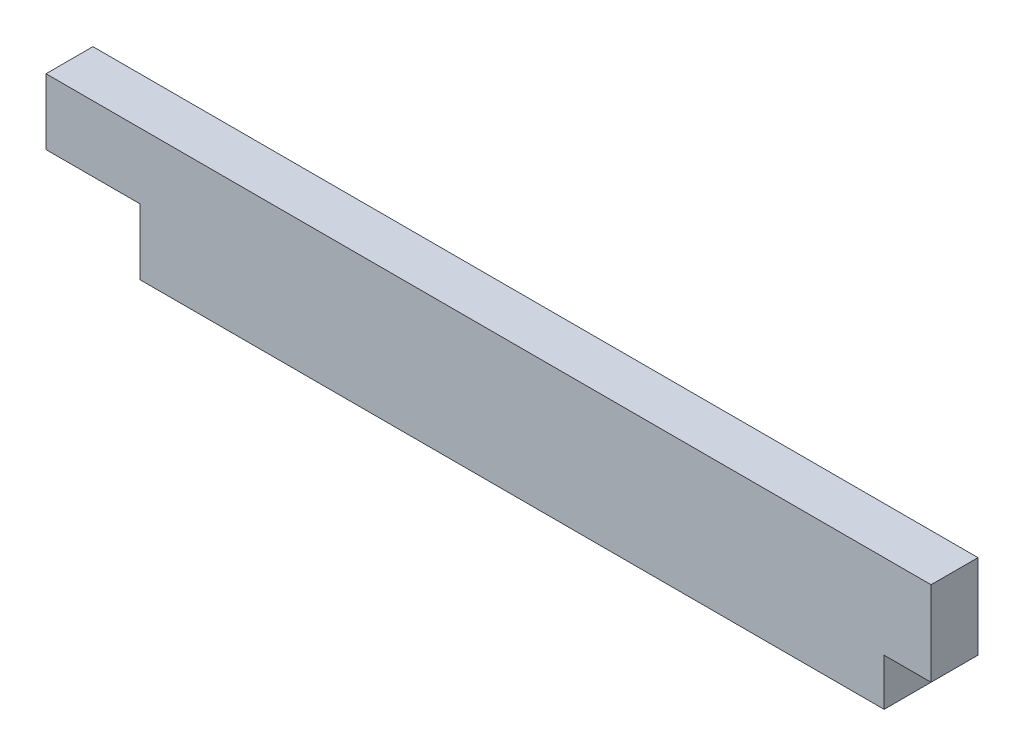
SolidWorks part; units mm, degrees
material "Сосна обыкновенная"
ref_plane "Front Plane" through (0, 0, 0) normal (0, 0, 1) x (1, 0, 0)
ref_plane "Top Plane" through (0, 0, 0) normal (0, 1, 0) x (1, 0, 0)
ref_plane "Right Plane" through (0, 0, 0) normal (1, 0, 0) x (0, 0, -1)
sketch "Эскиз1" plane through (0, 0, 0) normal (0, 0, 1) x (1, 0, 0)
  line L0 (-26.4, 0) -> (-20.8, 0)
  line L1 (-20.8, -3.92) -> (23.6, -3.92)
  line L2 (-26.4, 0) -> (-26.4, 3.92)
  line L3 (-26.4, 3.92) -> (26.4, 3.92)
  line L4 (26.4, -1.12) -> (26.4, 3.92)
  line L5 (-26.4, -3.92) -> (26.4, 3.92) construction
  line L6 (-26.4, 3.92) -> (26.4, -3.92) construction
  line L7 (-20.8, 0) -> (-20.8, -3.92)
  line L8 (26.4, -1.12) -> (23.6, -1.12)
  line L9 (23.6, -1.12) -> (23.6, -3.92)
  point P0 (0, 0)
  dimension "D1" = 7.84
  dimension "D2" = 52.8
  dimension "D3" = 3.92
  dimension "D4" = 5.6
  dimension "D5" = 2.8
  dimension "D6" = 2.8
extrude "Бобышка-Вытянуть1" add sketch "Эскиз1" along normal mid plane 2.8
equation "\"thickness\"= 2.8"
equation "\"D1@Эскиз1\"=\"thickness\"+\"thickness\"*1.8"
equation "\"D2@Эскиз1\"=\"thickness\"+50"
equation "\"D3@Эскиз1\"=\"D1@Эскиз1\"/2"
equation "\"D4@Эскиз1\"=\"thickness\"*2"
equation "\"D5@Эскиз1\"=\"thickness\""
equation "\"D6@Эскиз1\"=\"thickness\""
equation "\"D1@Бобышка-Вытянуть1\"=\"thickness\""
